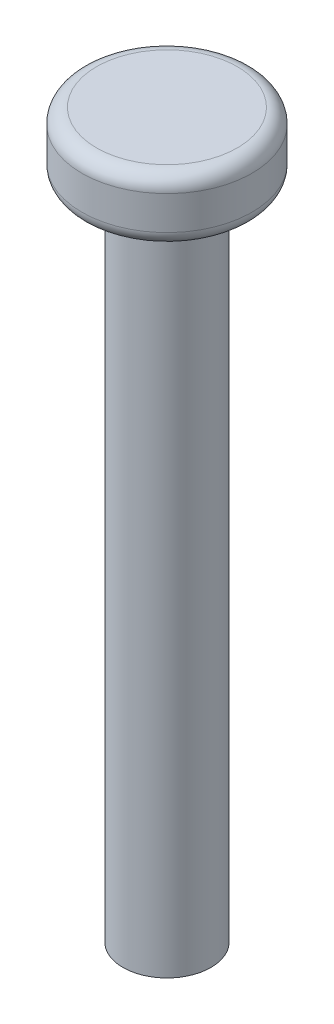
SolidWorks part; units mm, degrees
ref_plane "Спереди" through (0, 0, 0) normal (0, 0, 1) x (1, 0, 0)
ref_plane "Сверху" through (0, 0, 0) normal (0, 1, 0) x (1, 0, 0)
ref_plane "Справа" through (0, 0, 0) normal (1, 0, 0) x (0, 0, -1)
sketch "Sketch1" plane through (0, 0, 0) normal (0, 1, 0) x (1, 0, 0)
  circle A0 centre (0, 0) radius 3
  dimension "D1" = 6
extrude "Boss-Extrude1" add sketch "Sketch1" along normal blind 45
sketch "Sketch2" plane through (0, 45, 0) normal (0, 1, 0) x (1, 0, 0)
  circle A0 centre (0, 0) radius 5.8
  dimension "D1" = 11.6
extrude "Boss-Extrude2" add sketch "Sketch2" along normal blind 4.3
fillet "Fillet1" radius 1 2 edges at (0, 45, 5.8) (0, 49.3, 5.8)
